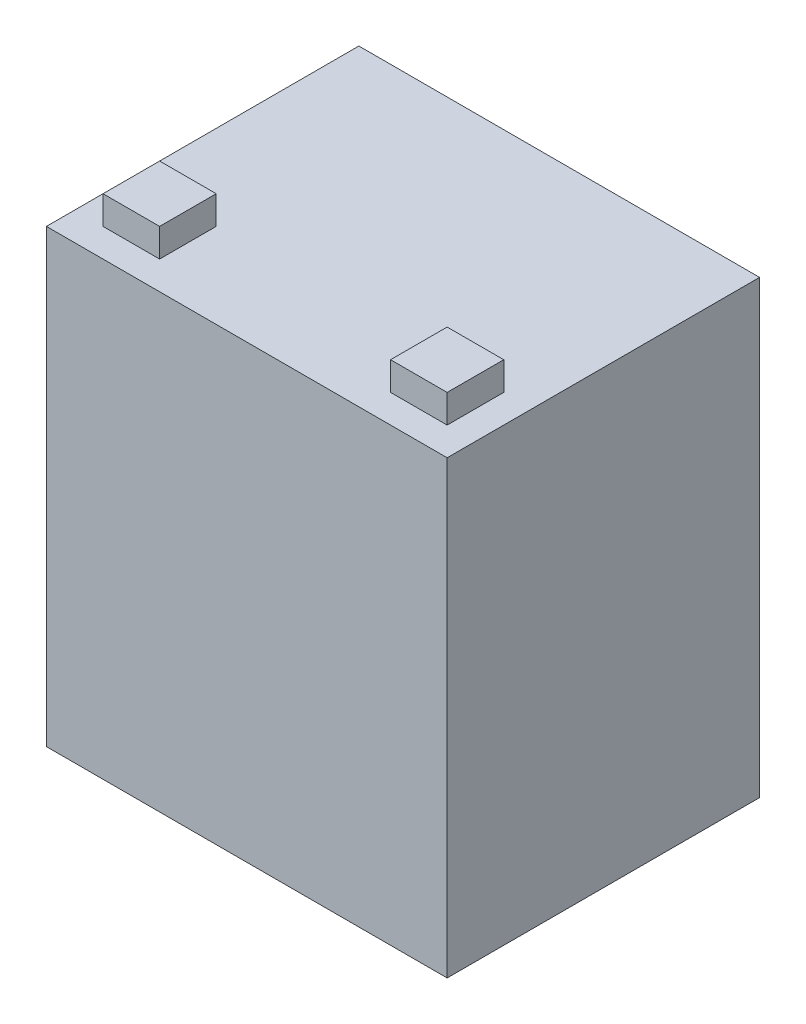
SolidWorks part; units mm, degrees
ref_plane "Front Plane" through (0, 0, 0) normal (0, 0, 1) x (1, 0, 0)
ref_plane "Top Plane" through (0, 0, 0) normal (0, 1, 0) x (1, 0, 0)
ref_plane "Right Plane" through (0, 0, 0) normal (1, 0, 0) x (0, 0, -1)
sketch "Sketch1" plane through (0, 0, 0) normal (0, 1, 0) x (1, 0, 0)
  line L1 (-44.958, -35.052) -> (44.958, -35.052)
  line L2 (-44.958, -35.052) -> (-44.958, 35.052)
  line L3 (-44.958, 35.052) -> (44.958, 35.052)
  line L4 (44.958, -35.052) -> (44.958, 35.052)
  line L5 (-44.958, -35.052) -> (44.958, 35.052) construction
  line L6 (-44.958, 35.052) -> (44.958, -35.052) construction
  point P0 (0, 0)
  dimension "D1" = 89.916
  dimension "D2" = 70.104
extrude "Boss-Extrude1" add sketch "Sketch1" along normal blind 101.092
sketch "Sketch3" plane through (0, 101.092, 0) normal (0, 1, 0) x (1, 0, 0)
  line L0 (-44.958, -35.052) -> (-38.608, -35.052) construction
  line L1 (-44.958, -35.052) -> (44.958, -35.052) construction
  line L2 (-44.958, -35.052) -> (-44.958, -28.702) construction
  line L3 (-44.958, 35.052) -> (-44.958, -35.052) construction
  line L4 (44.958, -35.052) -> (44.958, -28.702) construction
  line L5 (44.958, -35.052) -> (44.958, 35.052) construction
  line L6 (38.608, -28.702) -> (38.608, -16.002)
  line L7 (-38.608, -28.702) -> (-25.908, -28.702)
  line L8 (-38.608, -28.702) -> (-38.608, -16.002)
  line L9 (-38.608, -16.002) -> (-25.908, -16.002)
  line L10 (-25.908, -28.702) -> (-25.908, -16.002)
  line L11 (38.608, -28.702) -> (25.908, -28.702)
  line L12 (25.908, -28.702) -> (25.908, -16.002)
  line L13 (38.608, -16.002) -> (25.908, -16.002)
  line L14 (44.958, -35.052) -> (38.608, -35.052) construction
  line L15 (44.958, -28.702) -> (38.608, -28.702) construction
  line L16 (38.608, -35.052) -> (38.608, -28.702) construction
  dimension "D1" = 6.35
  dimension "D2" = 6.35
  dimension "D3" = 12.7
  dimension "D4" = 12.7
  dimension "D5" = 6.35
  dimension "D6" = 6.35
  dimension "D7" = 6.35
  dimension "D8" = 12.7
  dimension "D9" = 12.7
  dimension "D10" = 6.35
extrude "Boss-Extrude2" add sketch "Sketch3" along normal blind 6.35
